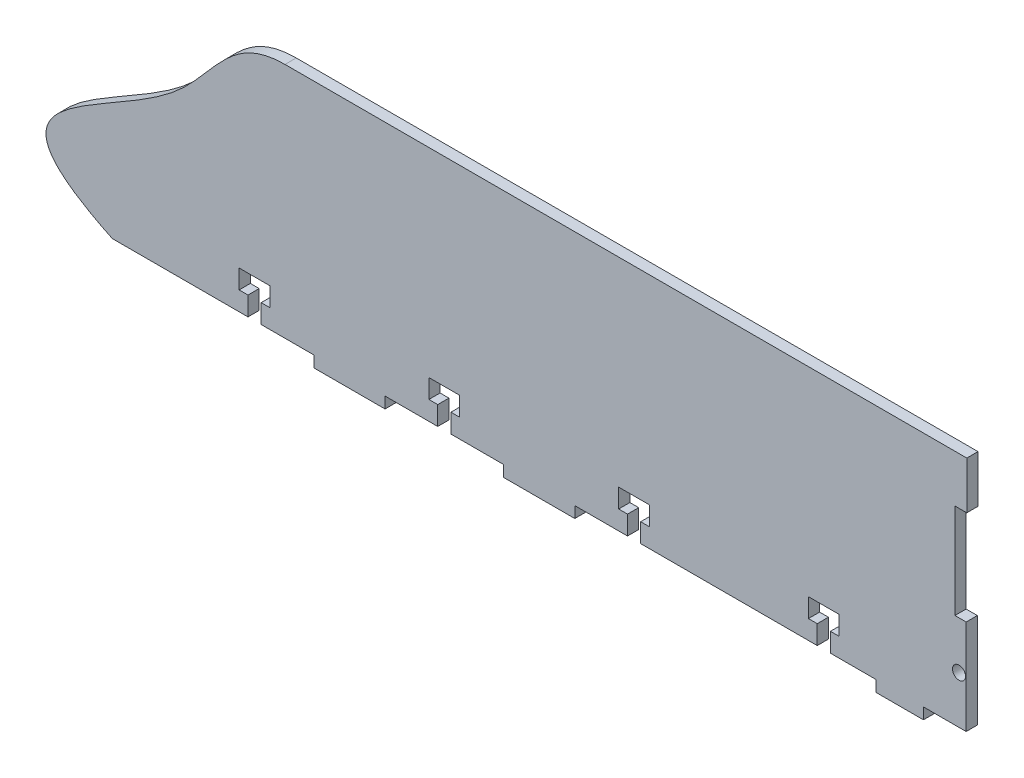
SolidWorks part; units mm, degrees
ref_plane "Front Plane" through (0, 0, 0) normal (0, 0, 1) x (1, 0, 0)
ref_plane "Top Plane" through (0, 0, 0) normal (0, 1, 0) x (1, 0, 0)
ref_plane "Right Plane" through (0, 0, 0) normal (1, 0, 0) x (0, 0, -1)
sketch "Sketch1" plane through (0, 0, 0) normal (0, 0, 1) x (1, 0, 0)
  line L0 (-76.2, -31.75) -> (-76.2, -10.2034) construction
  line L1 (-68.0501, 31.75) -> (111.125, 31.75)
  line L2 (111.125, 31.75) -> (114.475, 31.75)
  line L3 (-114.3, -31.75) -> (-77.9653, -31.75)
  line L4 (114.3, -18.2294) -> (114.3, -6.35)
  line L5 (-74.4347, -26.67) -> (-72.0725, -26.67)
  line L6 (-29.5275, -21.59) -> (-21.2725, -21.59)
  line L7 (-77.9653, -31.75) -> (-77.9653, -26.67)
  line L8 (-74.4347, -31.75) -> (-60.325, -31.75)
  line L9 (-74.4347, -31.75) -> (-74.4347, -26.67)
  line L10 (-80.3275, -26.67) -> (-77.9653, -26.67)
  line L11 (-80.3275, -26.67) -> (-80.3275, -21.59)
  line L12 (-80.3275, -21.59) -> (-72.0725, -21.59)
  line L13 (-72.0725, -26.67) -> (-72.0725, -21.59)
  line L14 (-21.2725, -26.67) -> (-21.2725, -21.59)
  line L15 (-23.6347, -26.67) -> (-21.2725, -26.67)
  line L16 (-29.5275, -26.67) -> (-27.1653, -26.67)
  line L17 (-27.1653, -31.75) -> (-27.1653, -26.67)
  line L18 (-23.6347, -31.75) -> (-23.6347, -26.67)
  line L19 (-29.5275, -26.67) -> (-29.5275, -21.59)
  line L20 (21.2725, -21.59) -> (29.5275, -21.59)
  line L21 (29.5275, -26.67) -> (29.5275, -21.59)
  line L22 (27.1653, -26.67) -> (29.5275, -26.67)
  line L23 (21.2725, -26.67) -> (23.6347, -26.67)
  line L24 (23.6347, -31.75) -> (23.6347, -26.67)
  line L25 (27.1653, -31.75) -> (27.1653, -26.67)
  line L26 (21.2725, -26.67) -> (21.2725, -21.59)
  line L27 (72.0725, -21.59) -> (80.3275, -21.59)
  line L28 (80.3275, -26.67) -> (80.3275, -21.59)
  line L29 (77.9653, -26.67) -> (80.3275, -26.67)
  line L30 (72.0725, -26.67) -> (74.4347, -26.67)
  line L31 (74.4347, -31.75) -> (74.4347, -26.67)
  line L32 (77.9653, -31.75) -> (77.9653, -26.67)
  line L33 (72.0725, -26.67) -> (72.0725, -21.59)
  line L34 (-23.6347, -31.75) -> (-9.525, -31.75)
  line L35 (27.1653, -31.75) -> (74.4347, -31.75)
  line L36 (77.9653, -31.75) -> (88.1951, -31.75)
  line L37 (114.475, 31.75) -> (114.475, 19.05)
  line L38 (111.125, -31.75) -> (114.3, -31.75)
  line L39 (114.3, -31.75) -> (114.3, -19.8706)
  line L40 (102.87, -31.75) -> (111.125, -31.75)
  line L41 (114.475, 19.05) -> (111.3, 19.05)
  line L42 (9.525, -31.75) -> (23.6347, -31.75)
  line L43 (114.3, -6.35) -> (111.3, -6.35)
  line L44 (111.3, 19.05) -> (111.3, -6.35)
  line L45 (-60.325, -31.75) -> (-60.325, -34.75)
  line L46 (-60.325, -34.75) -> (-41.275, -34.75)
  line L47 (-41.275, -31.75) -> (-41.275, -34.75)
  line L48 (-50.8, -31.75) -> (-41.275, -34.75) construction
  line L49 (-60.325, -34.75) -> (-50.8, -31.75) construction
  line L50 (-41.275, -31.75) -> (-27.1653, -31.75)
  line L51 (-9.525, -31.75) -> (-9.525, -34.75)
  line L52 (-9.525, -34.75) -> (9.525, -34.75)
  line L53 (9.525, -31.75) -> (9.525, -34.75)
  line L54 (0, -31.75) -> (9.525, -34.75) construction
  line L55 (-9.525, -34.75) -> (0, -31.75) construction
  line L56 (88.1951, -31.75) -> (90.17, -31.75)
  line L57 (114.3, -18.2294) -> (114.3, -19.8706)
  line L59 (90.17, -31.75) -> (90.17, -34.75)
  line L60 (90.17, -34.75) -> (102.87, -34.75)
  line L61 (102.87, -31.75) -> (102.87, -34.75)
  circle A1 centre (112.395, -19.05) radius 1.7526
  spline S0 degree 3 poles (-114.3, -31.75) (-155.0429, -12.2404) (-94.5489, -1.3775) (-82.5351, 31.7543) (-68.0501, 31.75) knots 0 0 0 0 0.655069 1 1 1 1
  point P49 (-50.8, -31.75)
  point P56 (0, -31.75)
  dimension "D14" = 228.6
  dimension "D15" = 3
  dimension "D13" = 1.905
  dimension "D2" = 31.75
  dimension "D3" = 63.5
  dimension "D4" = 3
  dimension "D5" = 25.4
  dimension "D6" = 5.08
  dimension "D7" = 5.08
  dimension "D8" = 3.5306
  dimension "D9" = 1.7653
  dimension "D10" = 8.255
  dimension "D11" = 4.1275
  dimension "D16" = 3
  dimension "D17" = 3
  dimension "D18" = 19.05
  dimension "D19" = 19.05
  dimension "D20" = 12.7
  dimension "D21" = 11.43
  dimension "D12" = 4
extrude "Boss-Extrude1" add sketch "Sketch1" along normal blind 3
